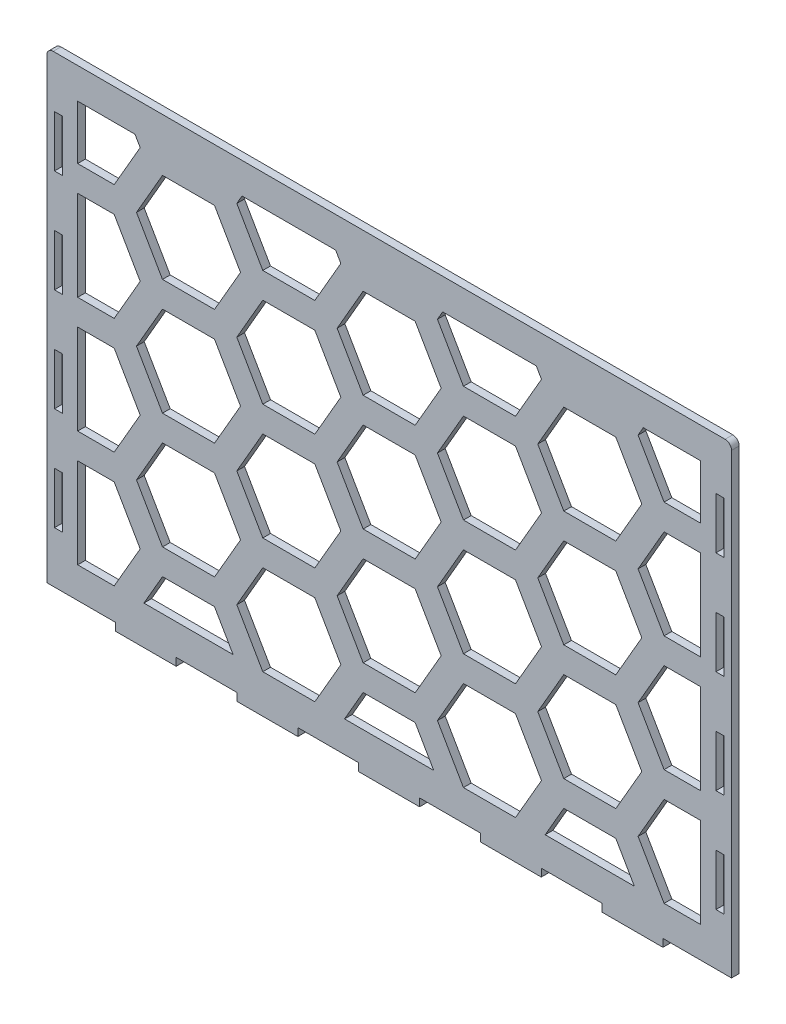
SolidWorks part; units mm, degrees
ref_plane "Front Plane" through (0, 0, 0) normal (0, 0, 1) x (1, 0, 0)
ref_plane "Top Plane" through (0, 0, 0) normal (0, 1, 0) x (1, 0, 0)
ref_plane "Right Plane" through (0, 0, 0) normal (1, 0, 0) x (0, 0, -1)
sketch "Sketch1" plane through (0, 0, 0) normal (0, 0, 1) x (1, 0, 0)
  line L0 (-130, -90) -> (-130, 90) construction
  line L1 (-133, -90) -> (133, -90)
  line L2 (-133, -90) -> (-133, 90)
  line L3 (-133, 90) -> (133, 90)
  line L4 (133, -90) -> (133, 90)
  line L5 (-133, -90) -> (133, 90) construction
  line L6 (-133, 90) -> (133, -90) construction
  line L7 (130, -90) -> (130, 90) construction
  line L8 (-82.7273, -93) -> (-59.0909, -93) construction
  line L9 (-11.8182, -93) -> (11.8182, -93)
  line L10 (-11.8182, -93) -> (-11.8182, -90)
  line L11 (-11.8182, -90) -> (11.8182, -90)
  line L12 (11.8182, -93) -> (11.8182, -90)
  line L13 (-11.8182, -93) -> (11.8182, -90) construction
  line L14 (-11.8182, -90) -> (11.8182, -93) construction
  line L15 (35.4545, -93) -> (59.0909, -93)
  line L16 (35.4545, -93) -> (35.4545, -90)
  line L17 (35.4545, -90) -> (59.0909, -90)
  line L18 (59.0909, -93) -> (59.0909, -90)
  line L19 (35.4545, -93) -> (59.0909, -90) construction
  line L20 (35.4545, -90) -> (59.0909, -93) construction
  line L21 (82.7273, -93) -> (106.3636, -93)
  line L22 (82.7273, -93) -> (82.7273, -90)
  line L23 (82.7273, -90) -> (106.3636, -90)
  line L24 (106.3636, -93) -> (106.3636, -90)
  line L25 (82.7273, -93) -> (106.3636, -90) construction
  line L26 (82.7273, -90) -> (106.3636, -93) construction
  line L27 (-59.0909, -93) -> (-35.4545, -93)
  line L28 (-59.0909, -93) -> (-59.0909, -90)
  line L29 (-59.0909, -90) -> (-35.4545, -90)
  line L30 (-35.4545, -93) -> (-35.4545, -90)
  line L31 (-59.0909, -93) -> (-35.4545, -90) construction
  line L32 (-59.0909, -90) -> (-35.4545, -93) construction
  line L33 (-106.3636, -93) -> (-82.7273, -93)
  line L34 (-106.3636, -93) -> (-106.3636, -90)
  line L35 (-106.3636, -90) -> (-82.7273, -90)
  line L36 (-82.7273, -93) -> (-82.7273, -90)
  line L37 (-106.3636, -93) -> (-82.7273, -90) construction
  line L38 (-106.3636, -90) -> (-82.7273, -93) construction
  line L39 (-35.4545, -93) -> (-11.8182, -93) construction
  line L40 (11.8182, -93) -> (35.4545, -93) construction
  line L41 (59.0909, -93) -> (82.7273, -93) construction
  line L42 (106.3636, -93) -> (130, -93) construction
  line L43 (-106.3636, -93) -> (-130, -93) construction
  line L44 (126.95, 90) -> (126.95, 70) construction
  line L45 (126.95, -10) -> (130, -10)
  line L46 (126.95, -10) -> (126.95, -30)
  line L47 (126.95, -30) -> (130, -30)
  line L48 (130, -10) -> (130, -30)
  line L49 (126.95, -10) -> (130, -30) construction
  line L50 (126.95, -30) -> (130, -10) construction
  line L51 (126.95, 10) -> (130, 10)
  line L52 (126.95, 10) -> (126.95, 30)
  line L53 (126.95, 30) -> (130, 30)
  line L54 (130, 10) -> (130, 30)
  line L55 (126.95, 10) -> (130, 30) construction
  line L56 (126.95, 30) -> (130, 10) construction
  line L57 (126.95, 50) -> (130, 50)
  line L58 (126.95, 50) -> (126.95, 70)
  line L59 (126.95, 70) -> (130, 70)
  line L60 (130, 50) -> (130, 70)
  line L61 (126.95, 50) -> (130, 70) construction
  line L62 (126.95, 70) -> (130, 50) construction
  line L63 (126.95, -50) -> (130, -50)
  line L64 (126.95, -50) -> (126.95, -70)
  line L65 (126.95, -70) -> (130, -70)
  line L66 (130, -50) -> (130, -70)
  line L67 (126.95, -50) -> (130, -70) construction
  line L68 (126.95, -70) -> (130, -50) construction
  line L69 (126.95, 50) -> (126.95, 30) construction
  line L70 (126.95, 10) -> (126.95, -10) construction
  line L71 (126.95, -30) -> (126.95, -50) construction
  line L72 (126.95, -70) -> (126.95, -90) construction
  line L73 (0, -781.5075) -> (0, 49218.4925) construction
  line L74 (-126.95, 70) -> (-130, 70)
  line L75 (-130, 50) -> (-130, 70)
  line L76 (-126.95, 50) -> (-130, 50)
  line L77 (-126.95, 50) -> (-126.95, 70)
  line L78 (-126.95, 30) -> (-130, 30)
  line L79 (-130, 10) -> (-130, 30)
  line L80 (-126.95, 10) -> (-130, 10)
  line L81 (-126.95, 10) -> (-126.95, 30)
  line L82 (-126.95, -30) -> (-130, -30)
  line L83 (-130, -10) -> (-130, -30)
  line L84 (-126.95, -10) -> (-130, -10)
  line L85 (-126.95, -10) -> (-126.95, -30)
  line L86 (-126.95, -70) -> (-130, -70)
  line L87 (-130, -50) -> (-130, -70)
  line L88 (-126.95, -50) -> (-130, -50)
  line L89 (-126.95, -50) -> (-126.95, -70)
  point P0 (0, 0)
  point P10 (0, -91.5)
  point P15 (47.2727, -91.5)
  point P20 (94.5455, -91.5)
  point P25 (-47.2727, -91.5)
  point P30 (-94.5455, -91.5)
  point P35 (128.475, 20)
  point P39 (128.475, -20)
  point P47 (128.475, 60)
  point P52 (128.475, -60)
  dimension "D1" = 266
  dimension "D2" = 180
  dimension "D5" = 3
  dimension "D6" = 3.05
  dimension "D3" = 3
  dimension "D4" = 3
extrude "Boss-Extrude1" add sketch "Sketch1" along normal blind 3 contours L1 L4 L3 L2 L81 L80 L79 L78 L77 L76 L75 L74 L60 L57 L58 L59 L54 L51 L52 L53 L45 L48 L47 L46 L63 L66 L65 L64 L84 L85 L82 L83 L88 | L33 L36 L1 L34 | L27 L30 L1 L28 | L9 L12 L1 L10 | L15 L18 L1 L16 | L24 L23 L22 L21
sketch "Sketch2" [suppressed] plane through (0, -93, 0) normal (0, 0, 1) x (1, 0, 0)
  line L1 (-234.6603, 8.6269) -> (-251.9808, 8.6269)
  line L2 (-251.9808, 8.6269) -> (-260.641, -6.3731)
  line L3 (-260.641, -6.3731) -> (-251.9808, -21.3731)
  line L4 (-251.9808, -21.3731) -> (-234.6603, -21.3731)
  line L5 (-234.6603, -21.3731) -> (-226, -6.3731)
  line L6 (-226, -6.3731) -> (-234.6603, 8.6269)
  line L7 (-192.6603, 8.6269) -> (-209.9808, 8.6269)
  line L8 (-209.9808, 8.6269) -> (-218.641, -6.3731)
  line L9 (-218.641, -6.3731) -> (-209.9808, -21.3731)
  line L10 (-209.9808, -21.3731) -> (-192.6603, -21.3731)
  line L11 (-192.6603, -21.3731) -> (-184, -6.3731)
  line L12 (-184, -6.3731) -> (-192.6603, 8.6269)
  line L13 (-150.6603, 8.6269) -> (-167.9808, 8.6269)
  line L14 (-167.9808, 8.6269) -> (-176.641, -6.3731)
  line L15 (-176.641, -6.3731) -> (-167.9808, -21.3731)
  line L16 (-167.9808, -21.3731) -> (-150.6603, -21.3731)
  line L17 (-150.6603, -21.3731) -> (-142, -6.3731)
  line L18 (-142, -6.3731) -> (-150.6603, 8.6269)
  line L19 (-108.6603, 8.6269) -> (-125.9808, 8.6269)
  line L20 (-125.9808, 8.6269) -> (-134.641, -6.3731)
  line L21 (-134.641, -6.3731) -> (-125.9808, -21.3731)
  line L22 (-125.9808, -21.3731) -> (-108.6603, -21.3731)
  line L23 (-108.6603, -21.3731) -> (-100, -6.3731)
  line L24 (-100, -6.3731) -> (-108.6603, 8.6269)
  line L25 (-66.6603, 8.6269) -> (-83.9808, 8.6269)
  line L26 (-83.9808, 8.6269) -> (-92.641, -6.3731)
  line L27 (-92.641, -6.3731) -> (-83.9808, -21.3731)
  line L28 (-83.9808, -21.3731) -> (-66.6603, -21.3731)
  line L29 (-66.6603, -21.3731) -> (-58, -6.3731)
  line L30 (-58, -6.3731) -> (-66.6603, 8.6269)
  line L31 (-24.6603, 8.6269) -> (-41.9808, 8.6269)
  line L32 (-41.9808, 8.6269) -> (-50.641, -6.3731)
  line L33 (-50.641, -6.3731) -> (-41.9808, -21.3731)
  line L34 (-41.9808, -21.3731) -> (-24.6603, -21.3731)
  line L35 (-24.6603, -21.3731) -> (-16, -6.3731)
  line L36 (-16, -6.3731) -> (-24.6603, 8.6269)
  line L37 (17.3397, 8.6269) -> (0.0192, 8.6269)
  line L38 (0.0192, 8.6269) -> (-8.641, -6.3731)
  line L39 (-8.641, -6.3731) -> (0.0192, -21.3731)
  line L40 (0.0192, -21.3731) -> (17.3397, -21.3731)
  line L41 (17.3397, -21.3731) -> (26, -6.3731)
  line L42 (26, -6.3731) -> (17.3397, 8.6269)
  line L43 (59.3397, 8.6269) -> (42.0192, 8.6269)
  line L44 (42.0192, 8.6269) -> (33.359, -6.3731)
  line L45 (33.359, -6.3731) -> (42.0192, -21.3731)
  line L46 (42.0192, -21.3731) -> (59.3397, -21.3731)
  line L47 (59.3397, -21.3731) -> (68, -6.3731)
  line L48 (68, -6.3731) -> (59.3397, 8.6269)
  line L49 (-171.6603, 45) -> (-188.9808, 45)
  line L50 (-188.9808, 45) -> (-197.641, 30)
  line L51 (-197.641, 30) -> (-188.9808, 15)
  line L52 (-188.9808, 15) -> (-171.6603, 15)
  line L53 (-171.6603, 15) -> (-163, 30)
  line L54 (-163, 30) -> (-171.6603, 45)
  line L55 (-129.6603, 45) -> (-146.9808, 45)
  line L56 (-146.9808, 45) -> (-155.641, 30)
  line L57 (-155.641, 30) -> (-146.9808, 15)
  line L58 (-146.9808, 15) -> (-129.6603, 15)
  line L59 (-129.6603, 15) -> (-121, 30)
  line L60 (-121, 30) -> (-129.6603, 45)
  line L61 (-87.6603, 45) -> (-104.9808, 45)
  line L62 (-104.9808, 45) -> (-113.641, 30)
  line L63 (-113.641, 30) -> (-104.9808, 15)
  line L64 (-104.9808, 15) -> (-87.6603, 15)
  line L65 (-87.6603, 15) -> (-79, 30)
  line L66 (-79, 30) -> (-87.6603, 45)
  line L67 (-45.6603, 45) -> (-62.9808, 45)
  line L68 (-62.9808, 45) -> (-71.641, 30)
  line L69 (-71.641, 30) -> (-62.9808, 15)
  line L70 (-62.9808, 15) -> (-45.6603, 15)
  line L71 (-45.6603, 15) -> (-37, 30)
  line L72 (-37, 30) -> (-45.6603, 45)
  line L73 (-3.6603, 45) -> (-20.9808, 45)
  line L74 (-20.9808, 45) -> (-29.641, 30)
  line L75 (-29.641, 30) -> (-20.9808, 15)
  line L76 (-20.9808, 15) -> (-3.6603, 15)
  line L77 (-3.6603, 15) -> (5, 30)
  line L78 (5, 30) -> (-3.6603, 45)
  line L79 (38.3397, 45) -> (21.0192, 45)
  line L80 (21.0192, 45) -> (12.359, 30)
  line L81 (12.359, 30) -> (21.0192, 15)
  line L82 (21.0192, 15) -> (38.3397, 15)
  line L83 (38.3397, 15) -> (47, 30)
  line L84 (47, 30) -> (38.3397, 45)
  line L85 (80.3397, 45) -> (63.0192, 45)
  line L86 (63.0192, 45) -> (54.359, 30)
  line L87 (54.359, 30) -> (63.0192, 15)
  line L88 (63.0192, 15) -> (80.3397, 15)
  line L89 (80.3397, 15) -> (89, 30)
  line L90 (89, 30) -> (80.3397, 45)
  line L91 (-150.6603, 81.3731) -> (-167.9808, 81.3731)
  line L92 (-167.9808, 81.3731) -> (-176.641, 66.3731)
  line L93 (-176.641, 66.3731) -> (-167.9808, 51.3731)
  line L94 (-167.9808, 51.3731) -> (-150.6603, 51.3731)
  line L95 (-150.6603, 51.3731) -> (-142, 66.3731)
  line L96 (-142, 66.3731) -> (-150.6603, 81.3731)
  line L97 (-108.6603, 81.3731) -> (-125.9808, 81.3731)
  line L98 (-125.9808, 81.3731) -> (-134.641, 66.3731)
  line L99 (-134.641, 66.3731) -> (-125.9808, 51.3731)
  line L100 (-125.9808, 51.3731) -> (-108.6603, 51.3731)
  line L101 (-108.6603, 51.3731) -> (-100, 66.3731)
  line L102 (-100, 66.3731) -> (-108.6603, 81.3731)
  line L103 (-66.6603, 81.3731) -> (-83.9808, 81.3731)
  line L104 (-83.9808, 81.3731) -> (-92.641, 66.3731)
  line L105 (-92.641, 66.3731) -> (-83.9808, 51.3731)
  line L106 (-83.9808, 51.3731) -> (-66.6603, 51.3731)
  line L107 (-66.6603, 51.3731) -> (-58, 66.3731)
  line L108 (-58, 66.3731) -> (-66.6603, 81.3731)
  line L109 (-24.6603, 81.3731) -> (-41.9808, 81.3731)
  line L110 (-41.9808, 81.3731) -> (-50.641, 66.3731)
  line L111 (-50.641, 66.3731) -> (-41.9808, 51.3731)
  line L112 (-41.9808, 51.3731) -> (-24.6603, 51.3731)
  line L113 (-24.6603, 51.3731) -> (-16, 66.3731)
  line L114 (-16, 66.3731) -> (-24.6603, 81.3731)
  line L115 (17.3397, 81.3731) -> (0.0192, 81.3731)
  line L116 (0.0192, 81.3731) -> (-8.641, 66.3731)
  line L117 (-8.641, 66.3731) -> (0.0192, 51.3731)
  line L118 (0.0192, 51.3731) -> (17.3397, 51.3731)
  line L119 (17.3397, 51.3731) -> (26, 66.3731)
  line L120 (26, 66.3731) -> (17.3397, 81.3731)
  line L121 (59.3397, 81.3731) -> (42.0192, 81.3731)
  line L122 (42.0192, 81.3731) -> (33.359, 66.3731)
  line L123 (33.359, 66.3731) -> (42.0192, 51.3731)
  line L124 (42.0192, 51.3731) -> (59.3397, 51.3731)
  line L125 (59.3397, 51.3731) -> (68, 66.3731)
  line L126 (68, 66.3731) -> (59.3397, 81.3731)
  line L127 (101.3397, 81.3731) -> (84.0192, 81.3731)
  line L128 (84.0192, 81.3731) -> (75.359, 66.3731)
  line L129 (75.359, 66.3731) -> (84.0192, 51.3731)
  line L130 (84.0192, 51.3731) -> (101.3397, 51.3731)
  line L131 (101.3397, 51.3731) -> (110, 66.3731)
  line L132 (110, 66.3731) -> (101.3397, 81.3731)
  line L133 (-129.6603, 117.7461) -> (-146.9808, 117.7461)
  line L134 (-146.9808, 117.7461) -> (-155.641, 102.7461)
  line L135 (-155.641, 102.7461) -> (-146.9808, 87.7461)
  line L136 (-146.9808, 87.7461) -> (-129.6603, 87.7461)
  line L137 (-129.6603, 87.7461) -> (-121, 102.7461)
  line L138 (-121, 102.7461) -> (-129.6603, 117.7461)
  line L139 (-87.6603, 117.7461) -> (-104.9808, 117.7461)
  line L140 (-104.9808, 117.7461) -> (-113.641, 102.7461)
  line L141 (-113.641, 102.7461) -> (-104.9808, 87.7461)
  line L142 (-104.9808, 87.7461) -> (-87.6603, 87.7461)
  line L143 (-87.6603, 87.7461) -> (-79, 102.7461)
  line L144 (-79, 102.7461) -> (-87.6603, 117.7461)
  line L145 (-45.6603, 117.7461) -> (-62.9808, 117.7461)
  line L146 (-62.9808, 117.7461) -> (-71.641, 102.7461)
  line L147 (-71.641, 102.7461) -> (-62.9808, 87.7461)
  line L148 (-62.9808, 87.7461) -> (-45.6603, 87.7461)
  line L149 (-45.6603, 87.7461) -> (-37, 102.7461)
  line L150 (-37, 102.7461) -> (-45.6603, 117.7461)
  line L151 (-3.6603, 117.7461) -> (-20.9808, 117.7461)
  line L152 (-20.9808, 117.7461) -> (-29.641, 102.7461)
  line L153 (-29.641, 102.7461) -> (-20.9808, 87.7461)
  line L154 (-20.9808, 87.7461) -> (-3.6603, 87.7461)
  line L155 (-3.6603, 87.7461) -> (5, 102.7461)
  line L156 (5, 102.7461) -> (-3.6603, 117.7461)
  line L157 (38.3397, 117.7461) -> (21.0192, 117.7461)
  line L158 (21.0192, 117.7461) -> (12.359, 102.7461)
  line L159 (12.359, 102.7461) -> (21.0192, 87.7461)
  line L160 (21.0192, 87.7461) -> (38.3397, 87.7461)
  line L161 (38.3397, 87.7461) -> (47, 102.7461)
  line L162 (47, 102.7461) -> (38.3397, 117.7461)
  line L163 (80.3397, 117.7461) -> (63.0192, 117.7461)
  line L164 (63.0192, 117.7461) -> (54.359, 102.7461)
  line L165 (54.359, 102.7461) -> (63.0192, 87.7461)
  line L166 (63.0192, 87.7461) -> (80.3397, 87.7461)
  line L167 (80.3397, 87.7461) -> (89, 102.7461)
  line L168 (89, 102.7461) -> (80.3397, 117.7461)
  line L169 (122.3397, 117.7461) -> (105.0192, 117.7461)
  line L170 (105.0192, 117.7461) -> (96.359, 102.7461)
  line L171 (96.359, 102.7461) -> (105.0192, 87.7461)
  line L172 (105.0192, 87.7461) -> (122.3397, 87.7461)
  line L173 (122.3397, 87.7461) -> (131, 102.7461)
  line L174 (131, 102.7461) -> (122.3397, 117.7461)
  line L175 (-108.6603, 154.1192) -> (-125.9808, 154.1192)
  line L176 (-125.9808, 154.1192) -> (-134.641, 139.1192)
  line L177 (-134.641, 139.1192) -> (-125.9808, 124.1192)
  line L178 (-125.9808, 124.1192) -> (-108.6603, 124.1192)
  line L179 (-108.6603, 124.1192) -> (-100, 139.1192)
  line L180 (-100, 139.1192) -> (-108.6603, 154.1192)
  line L181 (-66.6603, 154.1192) -> (-83.9808, 154.1192)
  line L182 (-83.9808, 154.1192) -> (-92.641, 139.1192)
  line L183 (-92.641, 139.1192) -> (-83.9808, 124.1192)
  line L184 (-83.9808, 124.1192) -> (-66.6603, 124.1192)
  line L185 (-66.6603, 124.1192) -> (-58, 139.1192)
  line L186 (-58, 139.1192) -> (-66.6603, 154.1192)
  line L187 (-24.6603, 154.1192) -> (-41.9808, 154.1192)
  line L188 (-41.9808, 154.1192) -> (-50.641, 139.1192)
  line L189 (-50.641, 139.1192) -> (-41.9808, 124.1192)
  line L190 (-41.9808, 124.1192) -> (-24.6603, 124.1192)
  line L191 (-24.6603, 124.1192) -> (-16, 139.1192)
  line L192 (-16, 139.1192) -> (-24.6603, 154.1192)
  line L193 (17.3397, 154.1192) -> (0.0192, 154.1192)
  line L194 (0.0192, 154.1192) -> (-8.641, 139.1192)
  line L195 (-8.641, 139.1192) -> (0.0192, 124.1192)
  line L196 (0.0192, 124.1192) -> (17.3397, 124.1192)
  line L197 (17.3397, 124.1192) -> (26, 139.1192)
  line L198 (26, 139.1192) -> (17.3397, 154.1192)
  line L199 (59.3397, 154.1192) -> (42.0192, 154.1192)
  line L200 (42.0192, 154.1192) -> (33.359, 139.1192)
  line L201 (33.359, 139.1192) -> (42.0192, 124.1192)
  line L202 (42.0192, 124.1192) -> (59.3397, 124.1192)
  line L203 (59.3397, 124.1192) -> (68, 139.1192)
  line L204 (68, 139.1192) -> (59.3397, 154.1192)
  line L205 (101.3397, 154.1192) -> (84.0192, 154.1192)
  line L206 (84.0192, 154.1192) -> (75.359, 139.1192)
  line L207 (75.359, 139.1192) -> (84.0192, 124.1192)
  line L208 (84.0192, 124.1192) -> (101.3397, 124.1192)
  line L209 (101.3397, 124.1192) -> (110, 139.1192)
  line L210 (110, 139.1192) -> (101.3397, 154.1192)
  line L211 (143.3397, 154.1192) -> (126.0192, 154.1192)
  line L212 (126.0192, 154.1192) -> (117.359, 139.1192)
  line L213 (117.359, 139.1192) -> (126.0192, 124.1192)
  line L214 (126.0192, 124.1192) -> (143.3397, 124.1192)
  line L215 (143.3397, 124.1192) -> (152, 139.1192)
  line L216 (152, 139.1192) -> (143.3397, 154.1192)
  line L217 (-87.6603, 190.4923) -> (-104.9808, 190.4923)
  line L218 (-104.9808, 190.4923) -> (-113.641, 175.4923)
  line L219 (-113.641, 175.4923) -> (-104.9808, 160.4923)
  line L220 (-104.9808, 160.4923) -> (-87.6603, 160.4923)
  line L221 (-87.6603, 160.4923) -> (-79, 175.4923)
  line L222 (-79, 175.4923) -> (-87.6603, 190.4923)
  line L223 (-45.6603, 190.4923) -> (-62.9808, 190.4923)
  line L224 (-62.9808, 190.4923) -> (-71.641, 175.4923)
  line L225 (-71.641, 175.4923) -> (-62.9808, 160.4923)
  line L226 (-62.9808, 160.4923) -> (-45.6603, 160.4923)
  line L227 (-45.6603, 160.4923) -> (-37, 175.4923)
  line L228 (-37, 175.4923) -> (-45.6603, 190.4923)
  line L229 (-3.6603, 190.4923) -> (-20.9808, 190.4923)
  line L230 (-20.9808, 190.4923) -> (-29.641, 175.4923)
  line L231 (-29.641, 175.4923) -> (-20.9808, 160.4923)
  line L232 (-20.9808, 160.4923) -> (-3.6603, 160.4923)
  line L233 (-3.6603, 160.4923) -> (5, 175.4923)
  line L234 (5, 175.4923) -> (-3.6603, 190.4923)
  line L235 (38.3397, 190.4923) -> (21.0192, 190.4923)
  line L236 (21.0192, 190.4923) -> (12.359, 175.4923)
  line L237 (12.359, 175.4923) -> (21.0192, 160.4923)
  line L238 (21.0192, 160.4923) -> (38.3397, 160.4923)
  line L239 (38.3397, 160.4923) -> (47, 175.4923)
  line L240 (47, 175.4923) -> (38.3397, 190.4923)
  line L241 (80.3397, 190.4923) -> (63.0192, 190.4923)
  line L242 (63.0192, 190.4923) -> (54.359, 175.4923)
  line L243 (54.359, 175.4923) -> (63.0192, 160.4923)
  line L244 (63.0192, 160.4923) -> (80.3397, 160.4923)
  line L245 (80.3397, 160.4923) -> (89, 175.4923)
  line L246 (89, 175.4923) -> (80.3397, 190.4923)
  line L247 (122.3397, 190.4923) -> (105.0192, 190.4923)
  line L248 (105.0192, 190.4923) -> (96.359, 175.4923)
  line L249 (96.359, 175.4923) -> (105.0192, 160.4923)
  line L250 (105.0192, 160.4923) -> (122.3397, 160.4923)
  line L251 (122.3397, 160.4923) -> (131, 175.4923)
  line L252 (131, 175.4923) -> (122.3397, 190.4923)
  line L253 (164.3397, 190.4923) -> (147.0192, 190.4923)
  line L254 (147.0192, 190.4923) -> (138.359, 175.4923)
  line L255 (138.359, 175.4923) -> (147.0192, 160.4923)
  line L256 (147.0192, 160.4923) -> (164.3397, 160.4923)
  line L257 (164.3397, 160.4923) -> (173, 175.4923)
  line L258 (173, 175.4923) -> (164.3397, 190.4923)
  line L343 (-213.6603, 45) -> (-230.9808, 45)
  line L344 (-230.9808, 45) -> (-239.641, 30)
  line L345 (-239.641, 30) -> (-230.9808, 15)
  line L346 (-230.9808, 15) -> (-213.6603, 15)
  line L347 (-213.6603, 15) -> (-205, 30)
  line L348 (-205, 30) -> (-213.6603, 45)
  line L349 (-192.6603, 81.3731) -> (-209.9808, 81.3731)
  line L350 (-209.9808, 81.3731) -> (-218.641, 66.3731)
  line L351 (-218.641, 66.3731) -> (-209.9808, 51.3731)
  line L352 (-209.9808, 51.3731) -> (-192.6603, 51.3731)
  line L353 (-192.6603, 51.3731) -> (-184, 66.3731)
  line L354 (-184, 66.3731) -> (-192.6603, 81.3731)
  line L355 (-171.6603, 117.7461) -> (-188.9808, 117.7461)
  line L356 (-188.9808, 117.7461) -> (-197.641, 102.7461)
  line L357 (-197.641, 102.7461) -> (-188.9808, 87.7461)
  line L358 (-188.9808, 87.7461) -> (-171.6603, 87.7461)
  line L359 (-171.6603, 87.7461) -> (-163, 102.7461)
  line L360 (-163, 102.7461) -> (-171.6603, 117.7461)
  line L361 (-150.6603, 154.1192) -> (-167.9808, 154.1192)
  line L362 (-167.9808, 154.1192) -> (-176.641, 139.1192)
  line L363 (-176.641, 139.1192) -> (-167.9808, 124.1192)
  line L364 (-167.9808, 124.1192) -> (-150.6603, 124.1192)
  line L365 (-150.6603, 124.1192) -> (-142, 139.1192)
  line L366 (-142, 139.1192) -> (-150.6603, 154.1192)
  line L367 (-129.6603, 190.4923) -> (-146.9808, 190.4923)
  line L368 (-146.9808, 190.4923) -> (-155.641, 175.4923)
  line L369 (-155.641, 175.4923) -> (-146.9808, 160.4923)
  line L370 (-146.9808, 160.4923) -> (-129.6603, 160.4923)
  line L371 (-129.6603, 160.4923) -> (-121, 175.4923)
  line L372 (-121, 175.4923) -> (-129.6603, 190.4923)
  line L387 (-226, -6.3731) -> (-218.641, -6.3731) construction
  line L388 (-209.9808, 8.6269) -> (-213.6603, 15) construction
  line L389 (-234.6603, 8.6269) -> (-230.9808, 15) construction
  line L390 (101.3397, 8.6269) -> (84.0192, 8.6269)
  line L391 (84.0192, 8.6269) -> (75.359, -6.3731)
  line L392 (75.359, -6.3731) -> (84.0192, -21.3731)
  line L393 (84.0192, -21.3731) -> (101.3397, -21.3731)
  line L394 (101.3397, -21.3731) -> (110, -6.3731)
  line L395 (110, -6.3731) -> (101.3397, 8.6269)
  line L396 (143.3397, 8.6269) -> (126.0192, 8.6269)
  line L397 (126.0192, 8.6269) -> (117.359, -6.3731)
  line L398 (117.359, -6.3731) -> (126.0192, -21.3731)
  line L399 (126.0192, -21.3731) -> (143.3397, -21.3731)
  line L400 (143.3397, -21.3731) -> (152, -6.3731)
  line L401 (152, -6.3731) -> (143.3397, 8.6269)
  line L402 (185.3397, 8.6269) -> (168.0192, 8.6269)
  line L403 (168.0192, 8.6269) -> (159.359, -6.3731)
  line L404 (159.359, -6.3731) -> (168.0192, -21.3731)
  line L405 (168.0192, -21.3731) -> (185.3397, -21.3731)
  line L406 (185.3397, -21.3731) -> (194, -6.3731)
  line L407 (194, -6.3731) -> (185.3397, 8.6269)
  line L414 (122.3397, 45) -> (105.0192, 45)
  line L415 (105.0192, 45) -> (96.359, 30)
  line L416 (96.359, 30) -> (105.0192, 15)
  line L417 (105.0192, 15) -> (122.3397, 15)
  line L418 (122.3397, 15) -> (131, 30)
  line L419 (131, 30) -> (122.3397, 45)
  line L420 (164.3397, 45) -> (147.0192, 45)
  line L421 (147.0192, 45) -> (138.359, 30)
  line L422 (138.359, 30) -> (147.0192, 15)
  line L423 (147.0192, 15) -> (164.3397, 15)
  line L424 (164.3397, 15) -> (173, 30)
  line L425 (173, 30) -> (164.3397, 45)
  line L426 (206.3397, 45) -> (189.0192, 45)
  line L427 (189.0192, 45) -> (180.359, 30)
  line L428 (180.359, 30) -> (189.0192, 15)
  line L429 (189.0192, 15) -> (206.3397, 15)
  line L430 (206.3397, 15) -> (215, 30)
  line L431 (215, 30) -> (206.3397, 45)
  line L438 (143.3397, 81.3731) -> (126.0192, 81.3731)
  line L439 (126.0192, 81.3731) -> (117.359, 66.3731)
  line L440 (117.359, 66.3731) -> (126.0192, 51.3731)
  line L441 (126.0192, 51.3731) -> (143.3397, 51.3731)
  line L442 (143.3397, 51.3731) -> (152, 66.3731)
  line L443 (152, 66.3731) -> (143.3397, 81.3731)
  line L444 (185.3397, 81.3731) -> (168.0192, 81.3731)
  line L445 (168.0192, 81.3731) -> (159.359, 66.3731)
  line L446 (159.359, 66.3731) -> (168.0192, 51.3731)
  line L447 (168.0192, 51.3731) -> (185.3397, 51.3731)
  line L448 (185.3397, 51.3731) -> (194, 66.3731)
  line L449 (194, 66.3731) -> (185.3397, 81.3731)
  line L450 (227.3397, 81.3731) -> (210.0192, 81.3731)
  line L451 (210.0192, 81.3731) -> (201.359, 66.3731)
  line L452 (201.359, 66.3731) -> (210.0192, 51.3731)
  line L453 (210.0192, 51.3731) -> (227.3397, 51.3731)
  line L454 (227.3397, 51.3731) -> (236, 66.3731)
  line L455 (236, 66.3731) -> (227.3397, 81.3731)
  line L462 (164.3397, 117.7461) -> (147.0192, 117.7461)
  line L463 (147.0192, 117.7461) -> (138.359, 102.7461)
  line L464 (138.359, 102.7461) -> (147.0192, 87.7461)
  line L465 (147.0192, 87.7461) -> (164.3397, 87.7461)
  line L466 (164.3397, 87.7461) -> (173, 102.7461)
  line L467 (173, 102.7461) -> (164.3397, 117.7461)
  line L468 (206.3397, 117.7461) -> (189.0192, 117.7461)
  line L469 (189.0192, 117.7461) -> (180.359, 102.7461)
  line L470 (180.359, 102.7461) -> (189.0192, 87.7461)
  line L471 (189.0192, 87.7461) -> (206.3397, 87.7461)
  line L472 (206.3397, 87.7461) -> (215, 102.7461)
  line L473 (215, 102.7461) -> (206.3397, 117.7461)
  line L474 (248.3397, 117.7461) -> (231.0192, 117.7461)
  line L475 (231.0192, 117.7461) -> (222.359, 102.7461)
  line L476 (222.359, 102.7461) -> (231.0192, 87.7461)
  line L477 (231.0192, 87.7461) -> (248.3397, 87.7461)
  line L478 (248.3397, 87.7461) -> (257, 102.7461)
  line L479 (257, 102.7461) -> (248.3397, 117.7461)
  line L486 (185.3397, 154.1192) -> (168.0192, 154.1192)
  line L487 (168.0192, 154.1192) -> (159.359, 139.1192)
  line L488 (159.359, 139.1192) -> (168.0192, 124.1192)
  line L489 (168.0192, 124.1192) -> (185.3397, 124.1192)
  line L490 (185.3397, 124.1192) -> (194, 139.1192)
  line L491 (194, 139.1192) -> (185.3397, 154.1192)
  line L492 (227.3397, 154.1192) -> (210.0192, 154.1192)
  line L493 (210.0192, 154.1192) -> (201.359, 139.1192)
  line L494 (201.359, 139.1192) -> (210.0192, 124.1192)
  line L495 (210.0192, 124.1192) -> (227.3397, 124.1192)
  line L496 (227.3397, 124.1192) -> (236, 139.1192)
  line L497 (236, 139.1192) -> (227.3397, 154.1192)
  line L498 (269.3397, 154.1192) -> (252.0192, 154.1192)
  line L499 (252.0192, 154.1192) -> (243.359, 139.1192)
  line L500 (243.359, 139.1192) -> (252.0192, 124.1192)
  line L501 (252.0192, 124.1192) -> (269.3397, 124.1192)
  line L502 (269.3397, 124.1192) -> (278, 139.1192)
  line L503 (278, 139.1192) -> (269.3397, 154.1192)
  line L510 (206.3397, 190.4923) -> (189.0192, 190.4923)
  line L511 (189.0192, 190.4923) -> (180.359, 175.4923)
  line L512 (180.359, 175.4923) -> (189.0192, 160.4923)
  line L513 (189.0192, 160.4923) -> (206.3397, 160.4923)
  line L514 (206.3397, 160.4923) -> (215, 175.4923)
  line L515 (215, 175.4923) -> (206.3397, 190.4923)
  line L516 (248.3397, 190.4923) -> (231.0192, 190.4923)
  line L517 (231.0192, 190.4923) -> (222.359, 175.4923)
  line L518 (222.359, 175.4923) -> (231.0192, 160.4923)
  line L519 (231.0192, 160.4923) -> (248.3397, 160.4923)
  line L520 (248.3397, 160.4923) -> (257, 175.4923)
  line L521 (257, 175.4923) -> (248.3397, 190.4923)
  line L522 (290.3397, 190.4923) -> (273.0192, 190.4923)
  line L523 (273.0192, 190.4923) -> (264.359, 175.4923)
  line L524 (264.359, 175.4923) -> (273.0192, 160.4923)
  line L525 (273.0192, 160.4923) -> (290.3397, 160.4923)
  line L526 (290.3397, 160.4923) -> (299, 175.4923)
  line L527 (299, 175.4923) -> (290.3397, 190.4923)
  line L534 (-121, 171) -> (-121, 15)
  line L535 (-121, 15) -> (121, 15)
  line L538 (121, 171) -> (-121, 171)
  line L544 (121, 171) -> (121, 15)
  line L551 (91.5, 131) -> (-91.5, 131)
  line L552 (-91.5, 131) -> (-91.5, 15)
  line L553 (-91.5, 15) -> (91.5, 15)
  line L554 (91.5, 15) -> (91.5, 131)
  line L560 (106.5, 171) -> (106.5, 15)
  line L561 (-106.5, 171) -> (-106.5, 15)
  circle A0 centre (-243.3205, -6.3731) radius 15 construction
fillet "Fillet1" radius 2.5 2 edges at (133, 90, 1.5) (-133, 90, 1.5)
sketch "Sketch3" plane through (0, 0, 0) normal (0, 0, -1) x (-1, 0, 0)
  line L0 (-145.7809, -20.5) -> (-165.9882, -20.5)
  line L1 (-145.7809, -65.5) -> (-165.9882, -65.5)
  line L2 (-165.9882, -65.5) -> (-176.0918, -83)
  line L3 (-176.0918, -83) -> (-165.9882, -100.5)
  line L4 (-165.9882, -100.5) -> (-145.7809, -100.5)
  line L5 (-145.7809, -100.5) -> (-135.6773, -83)
  line L6 (-135.6773, -83) -> (-145.7809, -65.5)
  line L13 (-165.9882, -20.5) -> (-176.0918, -38)
  line L14 (-137.1207, -105.5) -> (-127.0171, -123)
  line L15 (-127.0171, -123) -> (-106.8098, -123)
  line L16 (-106.8098, -123) -> (-96.7062, -105.5)
  line L17 (-96.7062, -105.5) -> (-106.8098, -88)
  line L18 (-106.8098, -88) -> (-127.0171, -88)
  line L19 (-127.0171, -88) -> (-137.1207, -105.5)
  line L20 (-176.0918, -38) -> (-165.9882, -55.5)
  line L21 (-165.9882, -55.5) -> (-145.7809, -55.5)
  line L22 (-145.7809, -55.5) -> (-135.6773, -38)
  line L23 (-135.6773, -38) -> (-145.7809, -20.5)
  line L24 (-137.1207, -60.5) -> (-127.0171, -78)
  line L25 (-127.0171, -78) -> (-106.8098, -78)
  line L26 (-106.8098, -78) -> (-96.7062, -60.5)
  line L27 (-96.7062, -60.5) -> (-106.8098, -43)
  line L28 (-106.8098, -43) -> (-127.0171, -43)
  line L29 (-127.0171, -43) -> (-137.1207, -60.5)
  line L30 (-145.7809, 24.5) -> (-165.9882, 24.5)
  line L31 (-165.9882, 24.5) -> (-176.0918, 7)
  line L32 (-176.0918, 7) -> (-165.9882, -10.5)
  line L33 (-165.9882, -10.5) -> (-145.7809, -10.5)
  line L34 (-145.7809, -10.5) -> (-135.6773, 7)
  line L35 (-135.6773, 7) -> (-145.7809, 24.5)
  line L36 (-137.1207, -15.5) -> (-127.0171, -33)
  line L37 (-127.0171, -33) -> (-106.8098, -33)
  line L38 (-106.8098, -33) -> (-96.7062, -15.5)
  line L39 (-96.7062, -15.5) -> (-106.8098, 2)
  line L40 (-106.8098, 2) -> (-127.0171, 2)
  line L41 (-127.0171, 2) -> (-137.1207, -15.5)
  line L42 (-145.7809, 69.5) -> (-165.9882, 69.5)
  line L43 (-165.9882, 69.5) -> (-176.0918, 52)
  line L44 (-176.0918, 52) -> (-165.9882, 34.5)
  line L45 (-165.9882, 34.5) -> (-145.7809, 34.5)
  line L46 (-145.7809, 34.5) -> (-135.6773, 52)
  line L47 (-135.6773, 52) -> (-145.7809, 69.5)
  line L48 (-137.1207, 29.5) -> (-127.0171, 12)
  line L49 (-127.0171, 12) -> (-106.8098, 12)
  line L50 (-106.8098, 12) -> (-96.7062, 29.5)
  line L51 (-96.7062, 29.5) -> (-106.8098, 47)
  line L52 (-106.8098, 47) -> (-127.0171, 47)
  line L53 (-127.0171, 47) -> (-137.1207, 29.5)
  line L54 (-145.7809, 114.5) -> (-165.9882, 114.5)
  line L55 (-165.9882, 114.5) -> (-176.0918, 97)
  line L56 (-176.0918, 97) -> (-165.9882, 79.5)
  line L57 (-165.9882, 79.5) -> (-145.7809, 79.5)
  line L58 (-145.7809, 79.5) -> (-135.6773, 97)
  line L59 (-135.6773, 97) -> (-145.7809, 114.5)
  line L60 (-137.1207, 74.5) -> (-127.0171, 57)
  line L61 (-127.0171, 57) -> (-106.8098, 57)
  line L62 (-106.8098, 57) -> (-96.7062, 74.5)
  line L63 (-96.7062, 74.5) -> (-106.8098, 92)
  line L64 (-106.8098, 92) -> (-127.0171, 92)
  line L65 (-127.0171, 92) -> (-137.1207, 74.5)
  line L66 (-145.7809, 159.5) -> (-165.9882, 159.5)
  line L67 (-165.9882, 159.5) -> (-176.0918, 142)
  line L68 (-176.0918, 142) -> (-165.9882, 124.5)
  line L69 (-165.9882, 124.5) -> (-145.7809, 124.5)
  line L70 (-145.7809, 124.5) -> (-135.6773, 142)
  line L71 (-135.6773, 142) -> (-145.7809, 159.5)
  line L72 (-137.1207, 119.5) -> (-127.0171, 102)
  line L73 (-127.0171, 102) -> (-106.8098, 102)
  line L74 (-106.8098, 102) -> (-96.7062, 119.5)
  line L75 (-96.7062, 119.5) -> (-106.8098, 137)
  line L76 (-106.8098, 137) -> (-127.0171, 137)
  line L77 (-127.0171, 137) -> (-137.1207, 119.5)
  line L102 (-145.7809, -65.5) -> (-145.7809, -20.5) construction
  line L103 (-127.0171, -88) -> (-127.0171, -78) construction
  line L104 (-140.7291, -74.25) -> (-132.0689, -69.25) construction
  line L105 (-59.1784, 119.5) -> (-49.0748, 102)
  line L106 (-49.0748, 102) -> (-28.8675, 102)
  line L107 (-28.8675, 102) -> (-18.7639, 119.5)
  line L108 (-18.7639, 119.5) -> (-28.8675, 137)
  line L109 (-28.8675, 137) -> (-49.0748, 137)
  line L110 (-49.0748, 137) -> (-59.1784, 119.5)
  line L111 (-67.8387, 159.5) -> (-88.0459, 159.5)
  line L112 (-88.0459, 159.5) -> (-98.1495, 142)
  line L113 (-98.1495, 142) -> (-88.0459, 124.5)
  line L114 (-88.0459, 124.5) -> (-67.8387, 124.5)
  line L115 (-67.8387, 124.5) -> (-57.735, 142)
  line L116 (-57.735, 142) -> (-67.8387, 159.5)
  line L117 (-67.8387, 114.5) -> (-88.0459, 114.5)
  line L118 (-88.0459, 114.5) -> (-98.1495, 97)
  line L119 (-98.1495, 97) -> (-88.0459, 79.5)
  line L120 (-88.0459, 79.5) -> (-67.8387, 79.5)
  line L121 (-67.8387, 79.5) -> (-57.735, 97)
  line L122 (-57.735, 97) -> (-67.8387, 114.5)
  line L123 (-67.8387, 69.5) -> (-88.0459, 69.5)
  line L124 (-88.0459, 69.5) -> (-98.1495, 52)
  line L125 (-98.1495, 52) -> (-88.0459, 34.5)
  line L126 (-88.0459, 34.5) -> (-67.8387, 34.5)
  line L127 (-67.8387, 34.5) -> (-57.735, 52)
  line L128 (-57.735, 52) -> (-67.8387, 69.5)
  line L129 (-67.8387, 24.5) -> (-88.0459, 24.5)
  line L130 (-88.0459, 24.5) -> (-98.1495, 7)
  line L131 (-98.1495, 7) -> (-88.0459, -10.5)
  line L132 (-88.0459, -10.5) -> (-67.8387, -10.5)
  line L133 (-67.8387, -10.5) -> (-57.735, 7)
  line L134 (-57.735, 7) -> (-67.8387, 24.5)
  line L135 (-59.1784, -15.5) -> (-49.0748, -33)
  line L136 (-49.0748, -33) -> (-28.8675, -33)
  line L137 (-28.8675, -33) -> (-18.7639, -15.5)
  line L138 (-18.7639, -15.5) -> (-28.8675, 2)
  line L139 (-28.8675, 2) -> (-49.0748, 2)
  line L140 (-49.0748, 2) -> (-59.1784, -15.5)
  line L141 (-67.8387, -20.5) -> (-88.0459, -20.5)
  line L142 (-88.0459, -20.5) -> (-98.1495, -38)
  line L143 (-98.1495, -38) -> (-88.0459, -55.5)
  line L144 (-88.0459, -55.5) -> (-67.8387, -55.5)
  line L145 (-67.8387, -55.5) -> (-57.735, -38)
  line L146 (-57.735, -38) -> (-67.8387, -20.5)
  line L147 (-59.1784, -60.5) -> (-49.0748, -78)
  line L148 (-49.0748, -78) -> (-28.8675, -78)
  line L149 (-28.8675, -78) -> (-18.7639, -60.5)
  line L150 (-18.7639, -60.5) -> (-28.8675, -43)
  line L151 (-28.8675, -43) -> (-49.0748, -43)
  line L152 (-49.0748, -43) -> (-59.1784, -60.5)
  line L153 (-67.8387, -65.5) -> (-88.0459, -65.5)
  line L154 (-88.0459, -65.5) -> (-98.1495, -83)
  line L155 (-98.1495, -83) -> (-88.0459, -100.5)
  line L156 (-88.0459, -100.5) -> (-67.8387, -100.5)
  line L157 (-67.8387, -100.5) -> (-57.735, -83)
  line L158 (-57.735, -83) -> (-67.8387, -65.5)
  line L159 (-59.1784, -105.5) -> (-49.0748, -123)
  line L160 (-49.0748, -123) -> (-28.8675, -123)
  line L161 (-28.8675, -123) -> (-18.7639, -105.5)
  line L162 (-18.7639, -105.5) -> (-28.8675, -88)
  line L163 (-28.8675, -88) -> (-49.0748, -88)
  line L164 (-49.0748, -88) -> (-59.1784, -105.5)
  line L165 (-59.1784, 29.5) -> (-49.0748, 12)
  line L166 (-49.0748, 12) -> (-28.8675, 12)
  line L167 (-28.8675, 12) -> (-18.7639, 29.5)
  line L168 (-18.7639, 29.5) -> (-28.8675, 47)
  line L169 (-28.8675, 47) -> (-49.0748, 47)
  line L170 (-49.0748, 47) -> (-59.1784, 29.5)
  line L171 (-59.1784, 74.5) -> (-49.0748, 57)
  line L172 (-49.0748, 57) -> (-28.8675, 57)
  line L173 (-28.8675, 57) -> (-18.7639, 74.5)
  line L174 (-18.7639, 74.5) -> (-28.8675, 92)
  line L175 (-28.8675, 92) -> (-49.0748, 92)
  line L176 (-49.0748, 92) -> (-59.1784, 74.5)
  line L177 (18.7639, 119.5) -> (28.8675, 102)
  line L178 (28.8675, 102) -> (49.0748, 102)
  line L179 (49.0748, 102) -> (59.1784, 119.5)
  line L180 (59.1784, 119.5) -> (49.0748, 137)
  line L181 (49.0748, 137) -> (28.8675, 137)
  line L182 (28.8675, 137) -> (18.7639, 119.5)
  line L183 (10.1036, 159.5) -> (-10.1036, 159.5)
  line L184 (-10.1036, 159.5) -> (-20.2073, 142)
  line L185 (-20.2073, 142) -> (-10.1036, 124.5)
  line L186 (-10.1036, 124.5) -> (10.1036, 124.5)
  line L187 (10.1036, 124.5) -> (20.2073, 142)
  line L188 (20.2073, 142) -> (10.1036, 159.5)
  line L189 (10.1036, 114.5) -> (-10.1036, 114.5)
  line L190 (-10.1036, 114.5) -> (-20.2073, 97)
  line L191 (-20.2073, 97) -> (-10.1036, 79.5)
  line L192 (-10.1036, 79.5) -> (10.1036, 79.5)
  line L193 (10.1036, 79.5) -> (20.2073, 97)
  line L194 (20.2073, 97) -> (10.1036, 114.5)
  line L195 (10.1036, 69.5) -> (-10.1036, 69.5)
  line L196 (-10.1036, 69.5) -> (-20.2073, 52)
  line L197 (-20.2073, 52) -> (-10.1036, 34.5)
  line L198 (-10.1036, 34.5) -> (10.1036, 34.5)
  line L199 (10.1036, 34.5) -> (20.2073, 52)
  line L200 (20.2073, 52) -> (10.1036, 69.5)
  line L201 (10.1036, 24.5) -> (-10.1036, 24.5)
  line L202 (-10.1036, 24.5) -> (-20.2073, 7)
  line L203 (-20.2073, 7) -> (-10.1036, -10.5)
  line L204 (-10.1036, -10.5) -> (10.1036, -10.5)
  line L205 (10.1036, -10.5) -> (20.2073, 7)
  line L206 (20.2073, 7) -> (10.1036, 24.5)
  line L207 (18.7639, -15.5) -> (28.8675, -33)
  line L208 (28.8675, -33) -> (49.0748, -33)
  line L209 (49.0748, -33) -> (59.1784, -15.5)
  line L210 (59.1784, -15.5) -> (49.0748, 2)
  line L211 (49.0748, 2) -> (28.8675, 2)
  line L212 (28.8675, 2) -> (18.7639, -15.5)
  line L213 (10.1036, -20.5) -> (-10.1036, -20.5)
  line L214 (-10.1036, -20.5) -> (-20.2073, -38)
  line L215 (-20.2073, -38) -> (-10.1036, -55.5)
  line L216 (-10.1036, -55.5) -> (10.1036, -55.5)
  line L217 (10.1036, -55.5) -> (20.2073, -38)
  line L218 (20.2073, -38) -> (10.1036, -20.5)
  line L219 (18.7639, -60.5) -> (28.8675, -78)
  line L220 (28.8675, -78) -> (49.0748, -78)
  line L221 (49.0748, -78) -> (59.1784, -60.5)
  line L222 (59.1784, -60.5) -> (49.0748, -43)
  line L223 (49.0748, -43) -> (28.8675, -43)
  line L224 (28.8675, -43) -> (18.7639, -60.5)
  line L225 (10.1036, -65.5) -> (-10.1036, -65.5)
  line L226 (-10.1036, -65.5) -> (-20.2073, -83)
  line L227 (-20.2073, -83) -> (-10.1036, -100.5)
  line L228 (-10.1036, -100.5) -> (10.1036, -100.5)
  line L229 (10.1036, -100.5) -> (20.2073, -83)
  line L230 (20.2073, -83) -> (10.1036, -65.5)
  line L231 (18.7639, -105.5) -> (28.8675, -123)
  line L232 (28.8675, -123) -> (49.0748, -123)
  line L233 (49.0748, -123) -> (59.1784, -105.5)
  line L234 (59.1784, -105.5) -> (49.0748, -88)
  line L235 (49.0748, -88) -> (28.8675, -88)
  line L236 (28.8675, -88) -> (18.7639, -105.5)
  line L237 (18.7639, 29.5) -> (28.8675, 12)
  line L238 (28.8675, 12) -> (49.0748, 12)
  line L239 (49.0748, 12) -> (59.1784, 29.5)
  line L240 (59.1784, 29.5) -> (49.0748, 47)
  line L241 (49.0748, 47) -> (28.8675, 47)
  line L242 (28.8675, 47) -> (18.7639, 29.5)
  line L243 (18.7639, 74.5) -> (28.8675, 57)
  line L244 (28.8675, 57) -> (49.0748, 57)
  line L245 (49.0748, 57) -> (59.1784, 74.5)
  line L246 (59.1784, 74.5) -> (49.0748, 92)
  line L247 (49.0748, 92) -> (28.8675, 92)
  line L248 (28.8675, 92) -> (18.7639, 74.5)
  line L249 (96.7062, 119.5) -> (106.8098, 102)
  line L250 (106.8098, 102) -> (127.0171, 102)
  line L251 (127.0171, 102) -> (137.1207, 119.5)
  line L252 (137.1207, 119.5) -> (127.0171, 137)
  line L253 (127.0171, 137) -> (106.8098, 137)
  line L254 (106.8098, 137) -> (96.7062, 119.5)
  line L255 (88.0459, 159.5) -> (67.8387, 159.5)
  line L256 (67.8387, 159.5) -> (57.735, 142)
  line L257 (57.735, 142) -> (67.8387, 124.5)
  line L258 (67.8387, 124.5) -> (88.0459, 124.5)
  line L259 (88.0459, 124.5) -> (98.1495, 142)
  line L260 (98.1495, 142) -> (88.0459, 159.5)
  line L261 (88.0459, 114.5) -> (67.8387, 114.5)
  line L262 (67.8387, 114.5) -> (57.735, 97)
  line L263 (57.735, 97) -> (67.8387, 79.5)
  line L264 (67.8387, 79.5) -> (88.0459, 79.5)
  line L265 (88.0459, 79.5) -> (98.1495, 97)
  line L266 (98.1495, 97) -> (88.0459, 114.5)
  line L267 (88.0459, 69.5) -> (67.8387, 69.5)
  line L268 (67.8387, 69.5) -> (57.735, 52)
  line L269 (57.735, 52) -> (67.8387, 34.5)
  line L270 (67.8387, 34.5) -> (88.0459, 34.5)
  line L271 (88.0459, 34.5) -> (98.1495, 52)
  line L272 (98.1495, 52) -> (88.0459, 69.5)
  line L273 (88.0459, 24.5) -> (67.8387, 24.5)
  line L274 (67.8387, 24.5) -> (57.735, 7)
  line L275 (57.735, 7) -> (67.8387, -10.5)
  line L276 (67.8387, -10.5) -> (88.0459, -10.5)
  line L277 (88.0459, -10.5) -> (98.1495, 7)
  line L278 (98.1495, 7) -> (88.0459, 24.5)
  line L279 (96.7062, -15.5) -> (106.8098, -33)
  line L280 (106.8098, -33) -> (127.0171, -33)
  line L281 (127.0171, -33) -> (137.1207, -15.5)
  line L282 (137.1207, -15.5) -> (127.0171, 2)
  line L283 (127.0171, 2) -> (106.8098, 2)
  line L284 (106.8098, 2) -> (96.7062, -15.5)
  line L285 (88.0459, -20.5) -> (67.8387, -20.5)
  line L286 (67.8387, -20.5) -> (57.735, -38)
  line L287 (57.735, -38) -> (67.8387, -55.5)
  line L288 (67.8387, -55.5) -> (88.0459, -55.5)
  line L289 (88.0459, -55.5) -> (98.1495, -38)
  line L290 (98.1495, -38) -> (88.0459, -20.5)
  line L291 (96.7062, -60.5) -> (106.8098, -78)
  line L292 (106.8098, -78) -> (127.0171, -78)
  line L293 (127.0171, -78) -> (137.1207, -60.5)
  line L294 (137.1207, -60.5) -> (127.0171, -43)
  line L295 (127.0171, -43) -> (106.8098, -43)
  line L296 (106.8098, -43) -> (96.7062, -60.5)
  line L297 (88.0459, -65.5) -> (67.8387, -65.5)
  line L298 (67.8387, -65.5) -> (57.735, -83)
  line L299 (57.735, -83) -> (67.8387, -100.5)
  line L300 (67.8387, -100.5) -> (88.0459, -100.5)
  line L301 (88.0459, -100.5) -> (98.1495, -83)
  line L302 (98.1495, -83) -> (88.0459, -65.5)
  line L303 (96.7062, -105.5) -> (106.8098, -123)
  line L304 (106.8098, -123) -> (127.0171, -123)
  line L305 (127.0171, -123) -> (137.1207, -105.5)
  line L306 (137.1207, -105.5) -> (127.0171, -88)
  line L307 (127.0171, -88) -> (106.8098, -88)
  line L308 (106.8098, -88) -> (96.7062, -105.5)
  line L309 (96.7062, 29.5) -> (106.8098, 12)
  line L310 (106.8098, 12) -> (127.0171, 12)
  line L311 (127.0171, 12) -> (137.1207, 29.5)
  line L312 (137.1207, 29.5) -> (127.0171, 47)
  line L313 (127.0171, 47) -> (106.8098, 47)
  line L314 (106.8098, 47) -> (96.7062, 29.5)
  line L315 (96.7062, 74.5) -> (106.8098, 57)
  line L316 (106.8098, 57) -> (127.0171, 57)
  line L317 (127.0171, 57) -> (137.1207, 74.5)
  line L318 (137.1207, 74.5) -> (127.0171, 92)
  line L319 (127.0171, 92) -> (106.8098, 92)
  line L320 (106.8098, 92) -> (96.7062, 74.5)
  line L321 (-137.1207, 119.5) -> (-59.1784, 119.5) construction
  line L322 (-93.0977, -74.25) -> (-101.758, -69.25) construction
  line L323 (130.5, 90) -> (-130.5, 90) construction
  line L324 (-121, -78) -> (121, -78)
  line L325 (-121, -78) -> (-121, 78)
  line L326 (-121, 78) -> (121, 78)
  line L327 (121, -78) -> (121, 78)
  line L328 (-121, -78) -> (121, 78) construction
  line L329 (-121, 78) -> (121, -78) construction
  line L330 (133, -90) -> (133, 87.5) construction
  line L331 (-106.8098, -43) -> (-121, -43) construction
  line L332 (106.8098, -43) -> (121, -43) construction
  circle A0 centre (-155.8846, -83) radius 17.5 construction
  circle A1 centre (-116.9134, -105.5) radius 17.5 construction
  point P10 (-127.0171, -83)
  point P301 (0, 0)
  dimension "D3" = 35
  dimension "D2" = 45
  dimension "D5" = 12
  dimension "D6" = 12
  dimension "D1" = 6
  dimension "D4" = 4
extrude "Cut-Extrude1" cut sketch "Sketch3" against normal blind 10 contours L325 L25 L26 L27 L28 | L145 L146 L141 L142 L143 L144 | L325 L37 L38 L39 L40 | L325 L49 L50 L51 L52 | L326 L325 L61 L62 L63 | L127 L128 L123 L124 L125 L126 | L326 L176 L171 L172 L173 L174 | L169 L170 L165 L166 L167 L168 | L133 L134 L129 L130 L131 L132 | L139 L140 L135 L136 L137 L138 | L151 L152 L147 L148 L149 L150 | L154 L324 L158 L153 | L226 L324 L230 L225 | L223 L224 L219 L220 L221 L222 | L298 L324 L302 L297 | L292 L327 L295 L296 L291 | L289 L290 L285 L286 L287 L288 | L280 L327 L283 L284 L279 | L277 L278 L273 L274 L275 L276 | L310 L327 L313 L314 L309 | L271 L272 L267 L268 L269 L270 | L316 L327 L326 L320 L315 | L326 L248 L243 L244 L245 L246 | L199 L200 L195 L196 L197 L198 | L241 L242 L237 L238 L239 L240 | L205 L206 L201 L202 L203 L204 | L211 L212 L207 L208 L209 L210 | L217 L218 L213 L214 L215 L216
